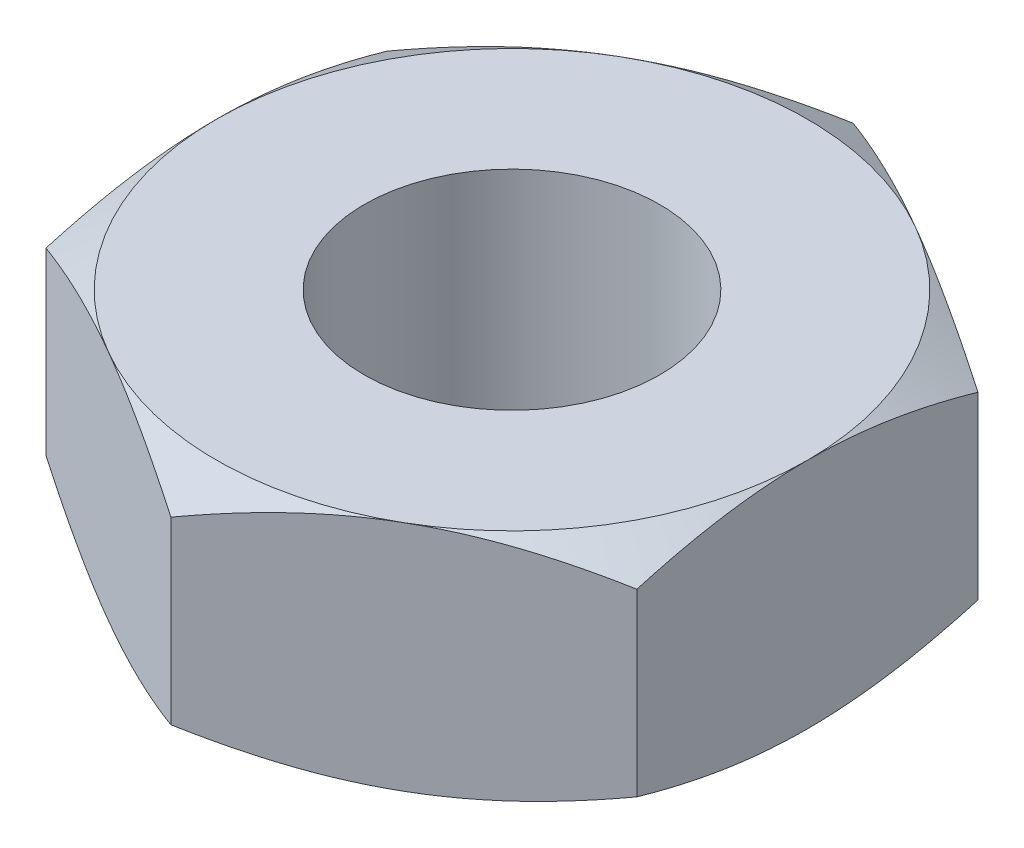
SolidWorks part; units mm, degrees
ref_plane "Front Plane" through (0, 0, 0) normal (0, 0, 1) x (1, 0, 0)
ref_plane "Top Plane" through (0, 0, 0) normal (0, 1, 0) x (1, 0, 0)
ref_plane "Right Plane" through (0, 0, 0) normal (1, 0, 0) x (0, 0, -1)
sketch "Sketch1" plane through (0, 0, 0) normal (0, 1, 0) x (1, 0, 0)
  line L1 (-12.7, -7.3323) -> (0, -14.6647)
  line L2 (0, -14.6647) -> (12.7, -7.3323)
  line L3 (12.7, -7.3323) -> (12.7, 7.3323)
  line L4 (12.7, 7.3323) -> (0, 14.6647)
  line L5 (0, 14.6647) -> (-12.7, 7.3323)
  line L6 (-12.7, 7.3323) -> (-12.7, -7.3323)
  circle A0 centre (0, 0) radius 12.7 construction
  dimension "D1" = 25.4
extrude "Boss-Extrude1" add sketch "Sketch1" along normal mid plane 10
sketch "Sketch2" plane through (0, 5, 0) normal (0, 1, 0) x (1, 0, 0)
  circle A0 centre (0, 0) radius 6.35
  dimension "D1" = 12.7
extrude "Cut-Extrude1" cut sketch "Sketch2" against normal through all
cosmetic thread "Cosmetic Thread1" parameters "D2"=14.2875
sketch "Sketch3" plane through (0, 5, 0) normal (0, 1, 0) x (1, 0, 0)
  circle A0 centre (0, 0) radius 12.7
extrude "Cut-Extrude2" cut sketch "Sketch3" against normal through all draft 60 flip side to cut
mirror "Mirror1" about plane through (0, 0, 0) normal (0, 1, 0) of "Cut-Extrude2"
